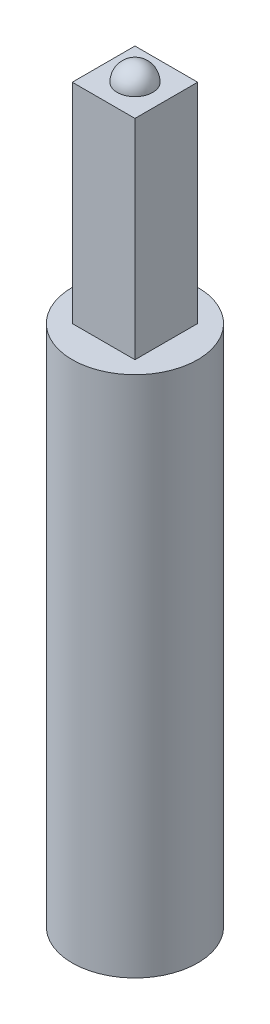
SolidWorks part; units mm, degrees
ref_plane "Front Plane" through (0, 0, 0) normal (0, 0, 1) x (1, 0, 0)
ref_plane "Top Plane" through (0, 0, 0) normal (0, 1, 0) x (1, 0, 0)
ref_plane "Right Plane" through (0, 0, 0) normal (1, 0, 0) x (0, 0, -1)
sketch "Sketch1" plane through (0, 0, 0) normal (0, 1, 0) x (1, 0, 0)
  circle A0 centre (0, 0) radius 30
  dimension "D1" = 60
extrude "Boss-Extrude1" add sketch "Sketch1" along normal blind 250
sketch "Sketch3" plane through (0, 250, 0) normal (0, 1, 0) x (1, 0, 0)
  line L0 (-15, 0.769) -> (-15, 15)
  line L1 (-15, 15) -> (15, 15)
  line L2 (15, 15) -> (15, -15)
  line L3 (15, -15) -> (-15, -15)
  line L4 (-15, -15) -> (-15, 0.769)
  dimension "D1" = 30
  dimension "D2" = 30
  dimension "D3" = 15
  dimension "D4" = 15
extrude "Boss-Extrude2" add sketch "Sketch3" along normal blind 100
sketch "Sketch4" plane through (0, 350, 0) normal (0, 1, 0) x (1, 0, 0)
  line L0 (0, 8.5) -> (0, -8.5)
  line L1 (15, 15) -> (-15, 15) construction
  arc A0 (0, 8.5) -> (0, -8.5) centre (0, 0) cw
  dimension "D1" = 6.5
  dimension "D2" = 17
revolve "Revolve1" add sketch "Sketch4" angle 360 about L0
